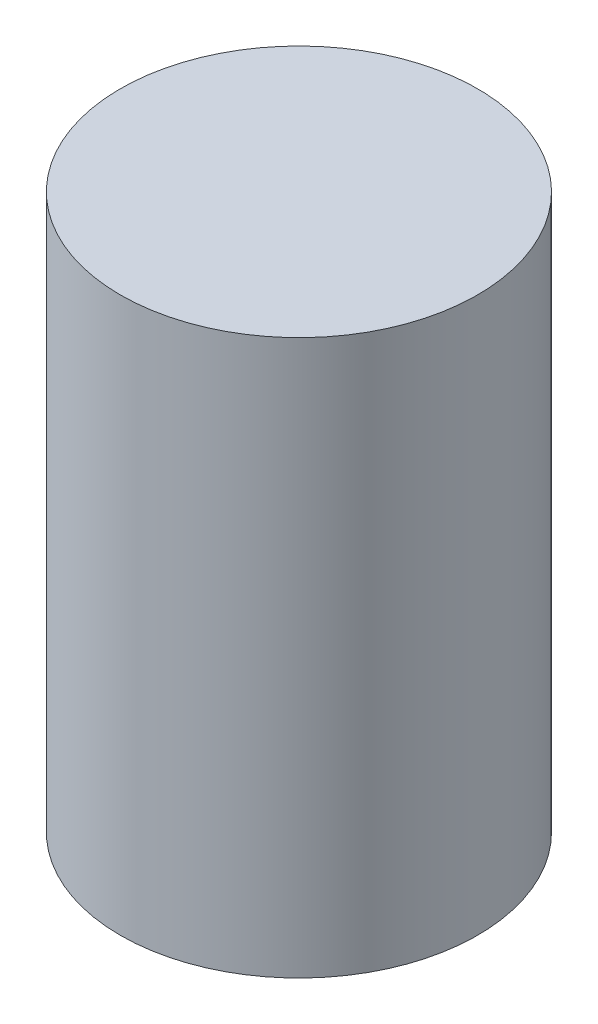
SolidWorks part; units mm, degrees
ref_plane "Front" through (0, 0, 0) normal (0, 0, 1) x (1, 0, 0)
ref_plane "Top" through (0, 0, 0) normal (0, 1, 0) x (1, 0, 0)
ref_plane "Right" through (0, 0, 0) normal (1, 0, 0) x (0, 0, -1)
sketch "Sketch1" plane through (0, 0, 0) normal (0, 1, 0) x (1, 0, 0)
  circle A0 centre (0, 0) radius 28.956
  dimension "D1" = 57.912
extrude "Boss-Extrude1" add sketch "Sketch1" along normal blind 89.916
